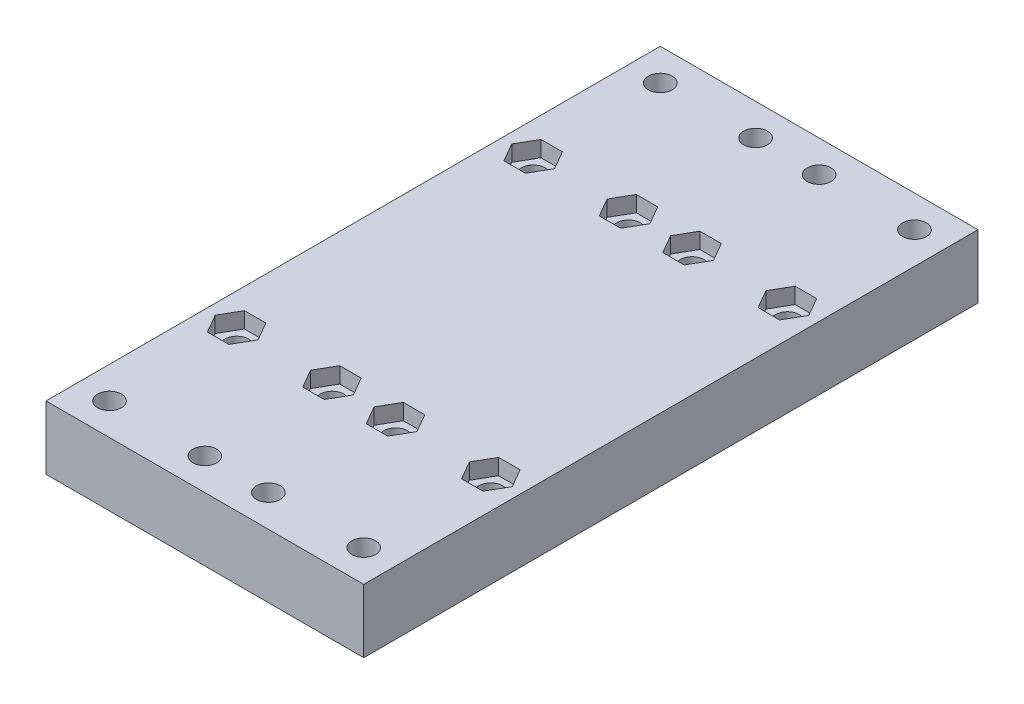
SolidWorks part; units mm, degrees
ref_plane "Front Plane" through (0, 0, 0) normal (0, 0, 1) x (1, 0, 0)
ref_plane "Top Plane" through (0, 0, 0) normal (0, 1, 0) x (1, 0, 0)
ref_plane "Right Plane" through (0, 0, 0) normal (1, 0, 0) x (0, 0, -1)
sketch "Sketch1" plane through (0, 0, 0) normal (0, 1, 0) x (1, 0, 0)
  line L1 (-30, -58) -> (30, -58)
  line L2 (-30, -58) -> (-30, 58)
  line L3 (-30, 58) -> (30, 58)
  line L4 (30, -58) -> (30, 58)
  line L5 (-30, -58) -> (30, 58) construction
  line L6 (-30, 58) -> (30, -58) construction
  point P0 (0, 0)
  dimension "D1" = 116
  dimension "D2" = 60
extrude "Boss-Extrude1" add sketch "Sketch1" along normal blind 12
sketch "Sketch2" plane through (0, 12, 0) normal (0, 1, 0) x (1, 0, 0)
  line L0 (30, 58) -> (-30, 58) construction
  line L1 (-30, 58) -> (-30, -58) construction
  line L2 (0, 58) -> (0, -58) construction
  line L3 (-30, -58) -> (30, -58) construction
  line L4 (-30, 0) -> (30, 0) construction
  line L5 (30, -58) -> (30, 58) construction
  circle A0 centre (-24, 52) radius 2.25
  circle A1 centre (-6, 52) radius 2.25
  circle A2 centre (-24, 28) radius 2.25
  circle A3 centre (-6, 28) radius 2.25
  circle A4 centre (6, 28) radius 2.25
  circle A5 centre (24, 28) radius 2.25
  circle A6 centre (6, 52) radius 2.25
  circle A7 centre (24, 52) radius 2.25
  circle A8 centre (24, -52) radius 2.25
  circle A9 centre (6, -52) radius 2.25
  circle A10 centre (24, -28) radius 2.25
  circle A11 centre (6, -28) radius 2.25
  circle A12 centre (-6, -28) radius 2.25
  circle A13 centre (-24, -28) radius 2.25
  circle A14 centre (-6, -52) radius 2.25
  circle A15 centre (-24, -52) radius 2.25
  dimension "D1" = 4.5
  dimension "D2" = 6
  dimension "D3" = 6
  dimension "D5" = 18
  dimension "D6" = 2
  dimension "D7" = 24
  dimension "D4" = 2
extrude "Cut-Extrude1" cut sketch "Sketch2" against normal up to next and the other way through all
sketch "Sketch3" plane through (0, 12, 0) normal (0, 1, 0) x (1, 0, 0)
  line L0 (0, -58) -> (0, 0) construction
  line L1 (-19.9585, -28) -> (-21.9793, -24.5)
  line L2 (-21.9793, -24.5) -> (-26.0207, -24.5)
  line L3 (-26.0207, -24.5) -> (-28.0415, -28)
  line L4 (-28.0415, -28) -> (-26.0207, -31.5)
  line L5 (-26.0207, -31.5) -> (-21.9793, -31.5)
  line L6 (-21.9793, -31.5) -> (-19.9585, -28)
  line L7 (-30, -58) -> (30, -58) construction
  line L8 (0, 0) -> (-30, 0) construction
  line L9 (-30, 58) -> (-30, -58) construction
  line L10 (-1.9585, -28) -> (-3.9793, -24.5)
  line L11 (-3.9793, -24.5) -> (-8.0207, -24.5)
  line L12 (-8.0207, -24.5) -> (-10.0415, -28)
  line L13 (-10.0415, -28) -> (-8.0207, -31.5)
  line L14 (-8.0207, -31.5) -> (-3.9793, -31.5)
  line L15 (-3.9793, -31.5) -> (-1.9585, -28)
  line L16 (3.9793, -31.5) -> (1.9585, -28)
  line L17 (8.0207, -31.5) -> (3.9793, -31.5)
  line L18 (10.0415, -28) -> (8.0207, -31.5)
  line L19 (8.0207, -24.5) -> (10.0415, -28)
  line L20 (3.9793, -24.5) -> (8.0207, -24.5)
  line L21 (1.9585, -28) -> (3.9793, -24.5)
  line L22 (21.9793, -31.5) -> (19.9585, -28)
  line L23 (26.0207, -31.5) -> (21.9793, -31.5)
  line L24 (28.0415, -28) -> (26.0207, -31.5)
  line L25 (26.0207, -24.5) -> (28.0415, -28)
  line L26 (21.9793, -24.5) -> (26.0207, -24.5)
  line L27 (19.9585, -28) -> (21.9793, -24.5)
  line L28 (26.0207, 31.5) -> (21.9793, 31.5)
  line L29 (28.0415, 28) -> (26.0207, 31.5)
  line L30 (26.0207, 24.5) -> (28.0415, 28)
  line L31 (21.9793, 24.5) -> (26.0207, 24.5)
  line L32 (19.9585, 28) -> (21.9793, 24.5)
  line L33 (21.9793, 31.5) -> (19.9585, 28)
  line L34 (8.0207, 31.5) -> (3.9793, 31.5)
  line L35 (10.0415, 28) -> (8.0207, 31.5)
  line L36 (8.0207, 24.5) -> (10.0415, 28)
  line L37 (3.9793, 24.5) -> (8.0207, 24.5)
  line L38 (1.9585, 28) -> (3.9793, 24.5)
  line L39 (3.9793, 31.5) -> (1.9585, 28)
  line L40 (-3.9793, 31.5) -> (-1.9585, 28)
  line L41 (-8.0207, 31.5) -> (-3.9793, 31.5)
  line L42 (-10.0415, 28) -> (-8.0207, 31.5)
  line L43 (-8.0207, 24.5) -> (-10.0415, 28)
  line L44 (-3.9793, 24.5) -> (-8.0207, 24.5)
  line L45 (-1.9585, 28) -> (-3.9793, 24.5)
  line L46 (-21.9793, 31.5) -> (-19.9585, 28)
  line L47 (-26.0207, 31.5) -> (-21.9793, 31.5)
  line L48 (-28.0415, 28) -> (-26.0207, 31.5)
  line L49 (-26.0207, 24.5) -> (-28.0415, 28)
  line L50 (-21.9793, 24.5) -> (-26.0207, 24.5)
  line L51 (-19.9585, 28) -> (-21.9793, 24.5)
  circle A0 centre (-24, -28) radius 3.5 construction
  dimension "D1" = 7
  dimension "D2" = 3.5
  dimension "D4" = 18
  dimension "D3" = 2
extrude "Cut-Extrude2" cut sketch "Sketch3" against normal blind 3 and the other way through all
